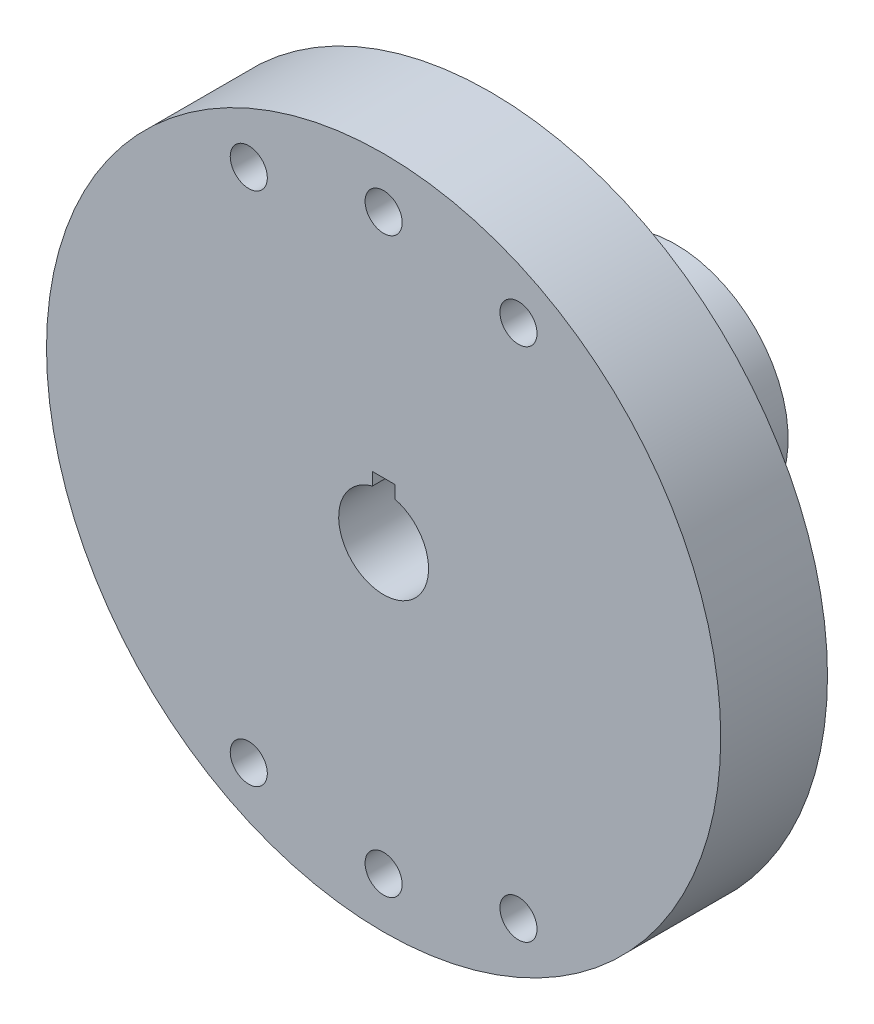
SolidWorks part; units mm, degrees
ref_plane "Front Plane" through (0, 0, 0) normal (0, 0, 1) x (1, 0, 0)
ref_plane "Top Plane" through (0, 0, 0) normal (0, 1, 0) x (1, 0, 0)
ref_plane "Right Plane" through (0, 0, 0) normal (1, 0, 0) x (0, 0, -1)
ref_plane "Plane1" through (0, 0, 0) normal (0, -1, 0) x (1, 0, 0)
sketch "Sketch1" plane through (0, 0, 0) normal (0, -1, 0) x (1, 0, 0)
  line L0 (30, 10) -> (0, 10)
  line L1 (0, 10) -> (0, 0.5)
  line L2 (0, 0.5) -> (30, 0.5)
  line L3 (30, 0.5) -> (30, 10)
  line L4 (0, 10) -> (0, 0.5) construction
revolve "Revolve1" add sketch "Sketch1" angle 360 about L4
sketch "Sketch2" plane through (0, 0, 0.5) normal (0, 0, -1) x (-1, 0, 0)
  arc A0 (1.9019, -26.9329) -> (10.5623, -24.8483) centre (0, 0) ccw
  arc A1 (10.5623, -24.8483) -> (14.3793, -22.8525) centre (12, -22.95) ccw
  arc A2 (14.3793, -22.8525) -> (14.3793, 22.8525) centre (0, 0) ccw
  arc A3 (14.3793, 22.8525) -> (10.5623, 24.8483) centre (12, 22.95) ccw
  arc A4 (10.5623, 24.8483) -> (1.9019, 26.9329) centre (0, 0) ccw
  arc A5 (1.9019, 26.9329) -> (-1.9019, 26.9329) centre (0, 25.5) ccw
  arc A6 (-1.9019, 26.9329) -> (-10.5623, 24.8483) centre (0, 0) ccw
  arc A7 (-10.5623, 24.8483) -> (-14.3793, 22.8525) centre (-12, 22.95) ccw
  arc A8 (-14.3793, 22.8525) -> (-14.3793, -22.8525) centre (0, 0) ccw
  arc A9 (-14.3793, -22.8525) -> (-10.5623, -24.8483) centre (-12, -22.95) ccw
  arc A10 (-10.5623, -24.8483) -> (-1.9019, -26.9329) centre (0, 0) ccw
  arc A11 (-1.9019, -26.9329) -> (1.9019, -26.9329) centre (0, -25.5) ccw
extrude "Cut-Extrude1" cut sketch "Sketch2" against normal blind 3.5
sketch "Sketch3" plane through (0, 0, 4) normal (0, 0, -1) x (-1, 0, 0)
  circle A0 centre (0, 0) radius 17.4
extrude "Boss-Extrude1" add sketch "Sketch3" along normal blind 4
sketch "Sketch4" plane through (0, 0, 0) normal (0, 0, -1) x (-1, 0, 0)
  circle A0 centre (0, 0) radius 10
extrude "Boss-Extrude2" add sketch "Sketch4" along normal blind 16
sketch "Sketch5" plane through (0, 0, 10) normal (0, 0, 1) x (1, 0, 0)
  line L0 (1, 5) -> (-1, 5)
  line L1 (-1, 5) -> (-1, 3.873)
  line L2 (1, 3.873) -> (1, 5)
  arc A0 (-1, 3.873) -> (1, 3.873) centre (0, 0) cw
extrude "Cut-Extrude2" cut sketch "Sketch5" against normal through all
sketch "Sketch6" plane through (0, 0, 0) normal (0, -1, 0) x (1, 0, 0)
  line L0 (4, 10) -> (0, 10)
  line L1 (0, 10) -> (0, -16)
  line L2 (0, -16) -> (4, -16)
  line L3 (4, -16) -> (4, 10)
  line L4 (0, 10) -> (0, -16) construction
revolve "Cut-Revolve1" cut sketch "Sketch6" angle 360 about L4
hole_wizard "#4 Clearance Hole1" positions "Sketch8" profile "Sketch7" hole size "#4" standard "ANSI Inch"
sketch "Sketch8" plane through (0, 0, 4) normal (0, 0, -1) x (-1, 0, 0)
  point P0 (12, -22.95)
  point P1 (0, -25.5)
  point P2 (-12, -22.95)
  point P3 (-12, 22.95)
  point P4 (0, 25.5)
  point P5 (12, 22.95)
sketch "Sketch7" plane through (-12, -22.95, 4) normal (1, 0, 0) x (0, 1, 0)
  line L0 (0, 0) -> (0, 6)
  line L1 (0, 6) -> (1.65, 6)
  line L2 (1.65, 6) -> (1.65, 0)
  line L5 (1.65, 0) -> (0, 0)
  line L11 (0, -6.35) -> (0, 107.95) construction
  dimension "Thru Hole Dia." = 3.3
  dimension "Thru Hole Depth" = 6
hole_wizard "#2 Clearance Hole1" positions "Sketch10" profile "Sketch9" hole size "#2" standard "ANSI Inch"
sketch "Sketch10" plane through (0, 0, -16) normal (0, 0, -1) x (-1, 0, 0)
  point P0 (-5.0558, -5.0558)
  point P1 (5.0558, -5.0558)
  point P2 (5.0558, 5.0558)
  point P3 (-5.0558, 5.0558)
sketch "Sketch9" plane through (5.0558, -5.0558, -16) normal (1, 0, 0) x (0, 1, 0)
  line L0 (0, 0) -> (0, 12)
  line L1 (0, 12) -> (1.25, 12)
  line L2 (1.25, 12) -> (1.25, 0)
  line L5 (1.25, 0) -> (0, 0)
  line L10 (0, 12) -> (-1.25, 12) construction
  line L11 (0, -6.35) -> (0, 107.95) construction
  dimension "Hole Dia." = 2.5
  dimension "Hole Depth" = 12
  dimension "Drill Angle" = 180
hole_wizard "#2 Clearance Hole2" positions "3DSketch1" profile "Sketch11" hole size "#2" standard "ANSI Inch"
sketch3d "3DSketch1"
  point P0 (0, -10, -6.2763)
sketch "Sketch11" plane through (0, -10, -6.2763) normal (1, 0, 0) x (0, 0, -1)
  line L0 (0, 0) -> (0, 6)
  line L1 (0, 6) -> (1.25, 6)
  line L2 (1.25, 6) -> (1.25, 0)
  line L5 (1.25, 0) -> (0, 0)
  line L11 (0, -6.35) -> (0, 107.95) construction
  dimension "Thru Hole Dia." = 2.5
  dimension "Thru Hole Depth" = 6
hole_wizard "#2 Clearance Hole3" positions "3DSketch2" profile "Sketch12" hole size "#2" standard "ANSI Inch"
sketch3d "3DSketch2"
  point P0 (0, 10, -6.2763)
sketch "Sketch12" plane through (0, 10, -6.2763) normal (1, 0, 0) x (0, 0, 1)
  line L0 (0, 0) -> (0, 40)
  line L1 (0, 40) -> (1.25, 40)
  line L2 (1.25, 40) -> (1.25, 0)
  line L5 (1.25, 0) -> (0, 0)
  line L11 (0, -6.35) -> (0, 107.95) construction
  dimension "Thru Hole Dia." = 2.5
  dimension "Thru Hole Depth" = 40
fillet "Fillet1" radius 3 1 edges at (-10, 0, 0)
